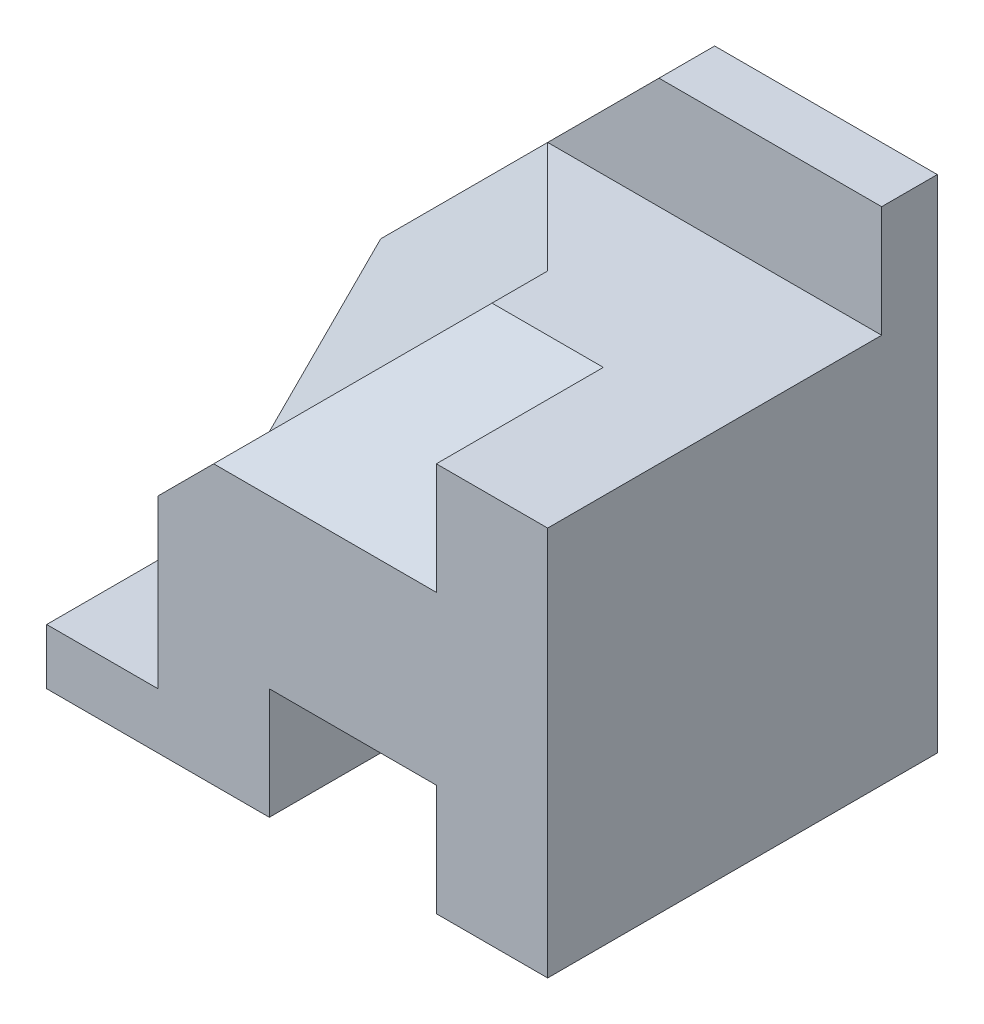
SolidWorks part; units mm, degrees
ref_plane "Front Plane" through (0, 0, 0) normal (0, 0, 1) x (1, 0, 0)
ref_plane "Top Plane" through (0, 0, 0) normal (0, 1, 0) x (1, 0, 0)
ref_plane "Right Plane" through (0, 0, 0) normal (1, 0, 0) x (0, 0, -1)
sketch "Sketch1" plane through (0, 0, 0) normal (0, 0, 1) x (1, 0, 0)
  line L0 (0, 4) -> (5, 9)
  line L1 (0, 0) -> (9, 0)
  line L2 (0, 0) -> (0, 4)
  line L3 (5, 9) -> (9, 9)
  line L4 (9, 0) -> (9, 9)
  point P2 (0, 9)
  dimension "D1" = 9
  dimension "D2" = 9
  dimension "D3" = 5
  dimension "D4" = 5
extrude "Boss-Extrude1" add sketch "Sketch1" along normal blind 1
sketch "Sketch2" plane through (0, 0, 1) normal (0, 0, 1) x (1, 0, 0)
  line L0 (9, 0) -> (9, 9) construction
  line L1 (9, 7) -> (0, 7)
  line L2 (9, 7) -> (9, 0)
  line L3 (9, 0) -> (0, 0)
  line L4 (0, 7) -> (0, 0)
  line L5 (9, 9) -> (5, 9) construction
  dimension "D1" = 2
extrude "Boss-Extrude2" add sketch "Sketch2" along normal blind 6
sketch3d "3DSketch1"
  line L0 (9, 7, 7) -> (9, 7, 1) construction
  line L1 (9, 7, 1) -> (3, 7, 1) construction
  line L2 (9, 0, 7) -> (9, 7, 7) construction
  line L3 (9, 7, 7) -> (0, 7, 7) construction
  line L4 (7, 7, 4) -> (7, 5, 7)
  line L5 (7, 5, 7) -> (3, 5, 7)
  line L6 (3, 5, 7) -> (5, 7, 4)
  line L7 (5, 7, 4) -> (7, 7, 4)
  point P0 (7, 7, 4)
  point P1 (7, 5, 7)
  point P2 (3, 5, 7)
  point P3 (5, 7, 4)
  dimension "D1" = 2
  dimension "D2" = 3
  dimension "D3" = 2
  dimension "D4" = 3
  dimension "D5" = 2
  dimension "D6" = 4
  dimension "D7" = 2
  dimension "D8" = 2
extrude "Cut-Extrude1" cut sketch "3DSketch1" along direction (0, -1, 0) on the side of the normal blind 6
sketch "Sketch4" plane through (0, 0, 7) normal (0, 0, 1) x (1, 0, 0)
  line L0 (0, 0) -> (9, 0) construction
  line L1 (4, 0) -> (7, 0)
  line L2 (4, 0) -> (4, 2)
  line L3 (4, 2) -> (7, 2)
  line L4 (7, 0) -> (7, 2)
  line L5 (9, 0) -> (9, 7) construction
  dimension "D1" = 2
  dimension "D2" = 3
  dimension "D3" = 2
extrude "Cut-Extrude3" cut sketch "Sketch4" against normal blind 7
sketch "Sketch5" plane through (0, 7, 0) normal (0, 1, 0) x (1, 0, 0)
  line L0 (0, -7) -> (0, -4)
  line L1 (0, -7) -> (0, -1) construction
  line L2 (0, -4) -> (2, -6)
  line L3 (2, -6) -> (2, -7)
  line L4 (3, -7) -> (0, -7) construction
  line L5 (2, -7) -> (0, -7)
  dimension "D1" = 1
  dimension "D2" = 2
extrude "Cut-Extrude5" cut sketch "Sketch5" against normal blind 6
sketch3d "3DSketch4"
  line L0 (2, 1, 7) -> (2, 7, 7) construction
  line L1 (2, 1, 6) -> (2, 7, 6) construction
  line L2 (0, 1, 4) -> (0, 7, 4) construction
  line L3 (0, 0, 7) -> (0, 0, 0) construction
  line L4 (3, 5, 7) -> (2, 4, 7)
  line L5 (0, 0, 7) -> (4, 0, 7) construction
  line L6 (9, 7, 1) -> (3, 7, 1) construction
  line L7 (9, 7, 7) -> (9, 7, 1) construction
  line L8 (5, 7, 3) -> (5, 7, 4)
  line L9 (5, 7, 4) -> (3, 5, 7)
  line L11 (2, 4, 6) -> (0, 2, 4)
  line L12 (0, 2, 4) -> (0, 2, 3)
  line L13 (0, 2, 3) -> (5, 7, 3)
  line L14 (2, 4, 7) -> (2, 4, 6)
  point P0 (3, 4, 7)
  point P1 (5, 7, 3)
  point P2 (2, 4, 7)
  point P3 (2, 4, 6)
  point P6 (0, 2, 4)
  point P9 (0, 2, 3)
  dimension "D1" = 1
  dimension "D2" = 2
  dimension "D3" = 2
  dimension "D4" = 3
  dimension "D5" = 3
  dimension "D6" = 1
  dimension "D7" = 4
  dimension "D8" = 2
  dimension "D9" = 4
extrude "Cut-Extrude6" cut sketch "3DSketch4" along direction (0, -1, 0) on the side against the normal blind 6
sketch3d "3DSketch5"
  line L0 (0, 2, 3) -> (0, 4, 1)
  line L1 (0, 4, 1) -> (3, 7, 1)
  line L2 (3, 7, 1) -> (5, 7, 3)
  line L3 (5, 7, 3) -> (0, 2, 3)
extrude "Cut-Extrude7" cut sketch "3DSketch5" along direction (0, -1, 0) on the side of the normal blind 6
